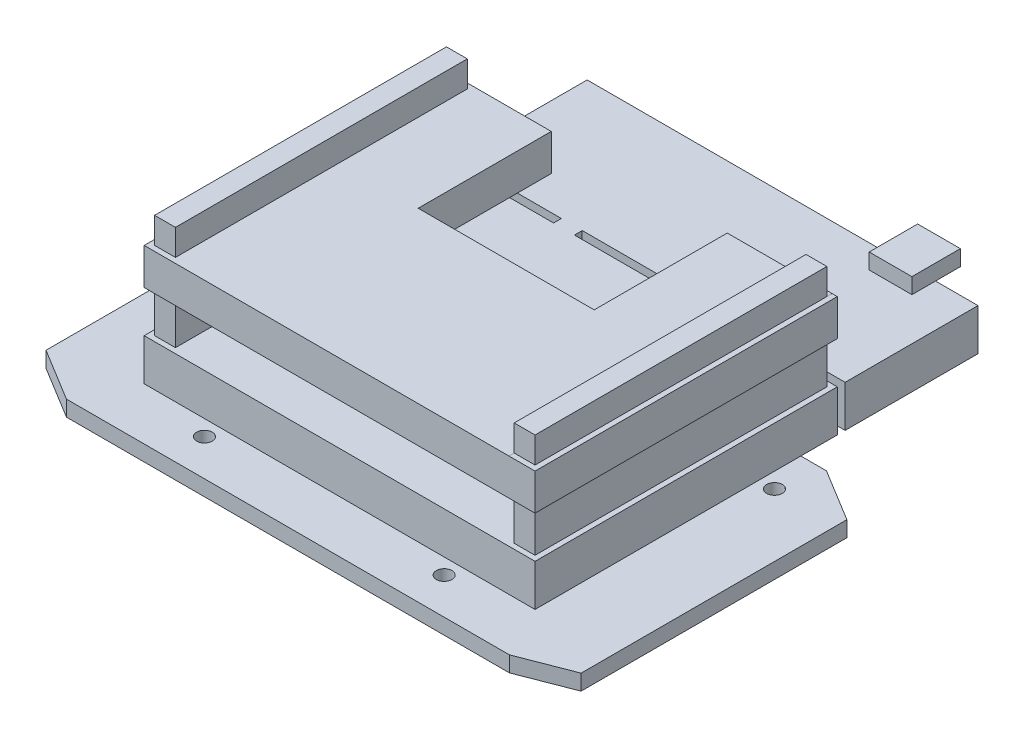
SolidWorks part; units mm, degrees
ref_plane "Front Plane" through (0, 0, 0) normal (0, 0, 1) x (1, 0, 0)
ref_plane "Top Plane" through (0, 0, 0) normal (0, 1, 0) x (1, 0, 0)
ref_plane "Right Plane" through (0, 0, 0) normal (1, 0, 0) x (0, 0, -1)
sketch "Esquisse1" plane through (0, 0, 0) normal (0, 1, 0) x (1, 0, 0)
  line L0 (-53.5603, 14.6941) -> (-43.6396, 18.5364)
  line L19 (41.3604, 18.5364) -> (51.4397, 12.3788)
  line L20 (51.4397, -38.6212) -> (41.5191, -42.4636)
  line L21 (-53.5603, -36.3059) -> (-43.4809, -42.4636)
  line L22 (-43.4809, -42.4636) -> (41.5191, -42.4636)
  line L23 (51.4397, -38.6212) -> (51.4397, 12.3788)
  line L24 (41.3604, 18.5364) -> (-43.6396, 18.5364)
  line L25 (-53.5603, 14.6941) -> (-53.5603, -36.3059)
  point P0 (0, 0)
  point P5 (0, 0)
  dimension "D1" = 105
  dimension "D2" = 85
  dimension "D3" = 85
  dimension "D4" = 51
  dimension "D5" = 51
  dimension "D7" = 61
extrude "Boss.-Extru.1" add sketch "Esquisse1" along normal blind 3
sketch "Esquisse2" plane through (0, 3, 0) normal (0, 1, 0) x (1, 0, 0)
  line L0 (-43.4809, -42.4636) -> (41.5191, -42.4636) construction
  line L1 (-0.9809, -42.4636) -> (-1.1396, 18.5364) construction
  line L2 (41.3604, 18.5364) -> (-43.6396, 18.5364) construction
  circle A0 centre (39.3813, 10.5364) radius 1.5
  circle A1 centre (-41.6187, 10.5364) radius 1.5
  circle A2 centre (-23.999, -35.4636) radius 1.5
  circle A3 centre (22.001, -35.4636) radius 1.5
  dimension "D1" = 3
  dimension "D2" = 3
  dimension "D3" = 3
  dimension "D4" = 3
  dimension "D5" = 7
  dimension "D6" = 7
  dimension "D7" = 46
  dimension "D8" = 23
  dimension "D9" = 81
  dimension "D10" = 40.5
  dimension "D11" = 8
  dimension "D12" = 8
extrude "Enlèv. mat.-Extru.1" cut sketch "Esquisse2" against normal blind 3
sketch "Esquisse3" plane through (0, 3, 0) normal (0, 1, 0) x (1, 0, 0)
  line L0 (-53.5603, 14.6941) -> (-53.5603, -36.3059) construction
  line L1 (-38.5603, -32.4636) -> (36.4397, -32.4636)
  line L2 (-38.5603, -32.4636) -> (-38.5603, 52.5364)
  line L3 (-38.5603, 52.5364) -> (36.4397, 52.5364)
  line L4 (36.4397, -32.4636) -> (36.4397, 52.5364)
  line L5 (-38.5603, -32.4636) -> (36.4397, 52.5364) construction
  line L6 (-38.5603, 52.5364) -> (36.4397, -32.4636) construction
  line L7 (-43.4809, -42.4636) -> (41.5191, -42.4636) construction
  line L8 (51.4397, -38.6212) -> (51.4397, 12.3788) construction
  point P0 (-1.0603, 10.0364)
  dimension "D1" = 85
  dimension "D2" = 75
  dimension "D3" = 15
  dimension "D4" = 10
  dimension "D5" = 15
extrude "Boss.-Extru.2" add sketch "Esquisse3" along normal blind 8
sketch "Esquisse5" plane through (0, 11, 0) normal (0, 1, 0) x (1, 0, 0)
  line L0 (36.4397, -32.4636) -> (36.4397, 52.5364) construction
  line L1 (-38.5603, -32.4636) -> (36.4397, -32.4636)
  line L2 (-38.5603, -32.4636) -> (-38.5603, 25.5364)
  line L3 (-38.5603, 25.5364) -> (36.4397, 25.5364)
  line L4 (36.4397, -32.4636) -> (36.4397, 25.5364)
  dimension "D1" = 58
extrude "Boss.-Extru.4" add sketch "Esquisse5" along normal blind 20
sketch "Esquisse6" plane through (0, 0, 0) normal (0, -1, 0) x (1, 0, 0)
  line L0 (51.4397, 13.1212) -> (-53.5603, 13.1212) construction
  line L1 (51.4397, 38.6212) -> (51.4397, -12.3788) construction
  line L2 (-53.5603, -14.6941) -> (-53.5603, 36.3059) construction
  circle A0 centre (-1.0603, 13.1212) radius 3.7838
extrude "Enlèv. mat.-Extru.2" cut sketch "Esquisse6" against normal blind 1
sketch "Esquisse8" plane through (0, 0, -25.5364) normal (0, 0, -1) x (-1, 0, 0)
  line L0 (-36.4397, 11) -> (38.5603, 11) construction
  line L1 (-31.4397, 11) -> (33.5603, 11)
  line L2 (-31.4397, 11) -> (-31.4397, 19)
  line L3 (-31.4397, 19) -> (33.5603, 19)
  line L4 (33.5603, 11) -> (33.5603, 19)
  line L5 (-36.4397, 31) -> (38.5603, 31) construction
  line L6 (-31.4397, 31) -> (33.5603, 31)
  line L7 (-31.4397, 31) -> (-31.4397, 26)
  line L8 (-31.4397, 26) -> (33.5603, 26)
  line L9 (33.5603, 31) -> (33.5603, 26)
  line L10 (-36.4397, 31) -> (-36.4397, 11) construction
  line L11 (38.5603, 31) -> (38.5603, 11) construction
  dimension "D1" = 5
  dimension "D2" = 8
  dimension "D3" = 5
  dimension "D4" = 5
  dimension "D5" = 5
  dimension "D6" = 5
extrude "Enlèv. mat.-Extru.3" cut sketch "Esquisse8" against normal blind 86
sketch "Esquisse9" plane through (-38.5603, 0, 0) normal (-1, 0, 0) x (0, 0, 1)
  line L0 (32.4636, 31) -> (32.4636, 3) construction
  line L1 (-25.5364, 11) -> (32.4636, 11)
  line L2 (-25.5364, 11) -> (-25.5364, 19)
  line L3 (-25.5364, 19) -> (32.4636, 19)
  line L4 (32.4636, 11) -> (32.4636, 19)
  line L6 (-25.5364, 31) -> (32.4636, 31)
  line L7 (-25.5364, 31) -> (-25.5364, 26)
  line L8 (-25.5364, 26) -> (32.4636, 26)
  line L9 (32.4636, 31) -> (32.4636, 26)
  dimension "D1" = 5
  dimension "D2" = 8
extrude "Enlèv. mat.-Extru.4" cut sketch "Esquisse9" against normal blind 1
sketch "Esquisse10" plane through (36.4397, 0, 0) normal (1, 0, 0) x (0, 0, -1)
  line L0 (25.5364, 31) -> (25.5364, 11) construction
  line L1 (-32.4636, 31) -> (25.5364, 31)
  line L2 (-32.4636, 31) -> (-32.4636, 25.9973)
  line L3 (-32.4636, 25.9973) -> (25.5364, 25.9973)
  line L4 (25.5364, 31) -> (25.5364, 25.9973)
  line L5 (-32.4636, 31) -> (-32.4636, 3) construction
  line L6 (25.5364, 11) -> (-32.4636, 11)
  line L7 (25.5364, 11) -> (25.5364, 19)
  line L8 (25.5364, 19) -> (-32.4636, 19)
  line L9 (-32.4636, 11) -> (-32.4636, 19)
  dimension "D1" = 5.0027
  dimension "D2" = 8
extrude "Enlèv. mat.-Extru.5" cut sketch "Esquisse10" against normal blind 1
sketch "Esquisse11" plane through (0, 0, -25.5364) normal (0, 0, -1) x (-1, 0, 0)
  line L1 (-35.4397, 31) -> (-31.4397, 31)
  line L2 (-35.4397, 31) -> (-35.4397, 26)
  line L3 (-35.4397, 26) -> (-31.4397, 26)
  line L4 (-31.4397, 31) -> (-31.4397, 26)
  line L5 (-35.4397, 19) -> (-31.4397, 19)
  line L6 (-35.4397, 19) -> (-35.4397, 11)
  line L7 (-35.4397, 11) -> (-31.4397, 11)
  line L8 (-31.4397, 19) -> (-31.4397, 11)
  line L9 (37.5603, 19) -> (33.5603, 19)
  line L10 (37.5603, 19) -> (37.5603, 11)
  line L11 (37.5603, 11) -> (33.5603, 11)
  line L12 (33.5603, 19) -> (33.5603, 11)
  line L13 (33.5603, 31) -> (37.5603, 31)
  line L14 (33.5603, 31) -> (33.5603, 26)
  line L15 (33.5603, 26) -> (37.5603, 26)
  line L16 (37.5603, 31) -> (37.5603, 26)
extrude "Enlèv. mat.-Extru.6" cut sketch "Esquisse11" against normal blind 1
sketch "Esquisse12" plane through (0, 0, 32.4636) normal (0, 0, 1) x (1, 0, 0)
  line L1 (-37.5603, 31) -> (-33.5603, 31)
  line L2 (-37.5603, 31) -> (-37.5603, 26)
  line L3 (-37.5603, 26) -> (-33.5603, 26)
  line L4 (-33.5603, 31) -> (-33.5603, 26)
  line L5 (-37.5603, 19) -> (-33.5603, 19)
  line L6 (-37.5603, 19) -> (-37.5603, 11)
  line L7 (-37.5603, 11) -> (-33.5603, 11)
  line L8 (-33.5603, 19) -> (-33.5603, 11)
  line L9 (31.4397, 31) -> (35.4397, 31)
  line L10 (31.4397, 31) -> (31.4397, 25.9973)
  line L11 (31.4397, 25.9973) -> (35.4397, 25.9973)
  line L12 (35.4397, 31) -> (35.4397, 25.9973)
  line L13 (31.4397, 19) -> (35.4397, 19)
  line L14 (31.4397, 19) -> (31.4397, 11)
  line L15 (31.4397, 11) -> (35.4397, 11)
  line L16 (35.4397, 19) -> (35.4397, 11)
extrude "Enlèv. mat.-Extru.7" cut sketch "Esquisse12" against normal blind 1
sketch "Esquisse13" plane through (0, 26, 0) normal (0, 1, 0) x (1, 0, 0)
  line L0 (35.4397, 25.5364) -> (-38.5603, 25.5364) construction
  line L1 (15.3267, 51.0728) -> (-18.4473, 51.0728)
  line L2 (15.3267, 51.0728) -> (15.3267, 0)
  line L3 (15.3267, 0) -> (-18.4473, 0)
  line L4 (-18.4473, 51.0728) -> (-18.4473, 0)
  line L5 (15.3267, 51.0728) -> (-18.4473, 0) construction
  line L6 (15.3267, 0) -> (-18.4473, 51.0728) construction
  point P0 (-1.5603, 25.5364)
extrude "Enlèv. mat.-Extru.8" cut sketch "Esquisse13" against normal blind 8
sketch "Esquisse14" plane through (0, 11, 0) normal (0, 1, 0) x (1, 0, 0)
  line L1 (-38.5603, 25.5364) -> (-18.0043, 25.5364)
  line L2 (-38.5603, 25.5364) -> (-38.5603, 27.0364)
  line L3 (-38.5603, 27.0364) -> (-18.0043, 27.0364)
  line L4 (-18.0043, 25.5364) -> (-18.0043, 27.0364)
  line L5 (36.4397, 25.5364) -> (14.5812, 25.5364)
  line L6 (36.4397, 25.5364) -> (36.4397, 27.0364)
  line L7 (36.4397, 27.0364) -> (14.5812, 27.0364)
  line L8 (14.5812, 25.5364) -> (14.5812, 27.0364)
  line L9 (-14.0043, 25.5364) -> (10.5812, 25.5364)
  line L10 (-14.0043, 25.5364) -> (-14.0043, 27.0364)
  line L11 (-14.0043, 27.0364) -> (10.5812, 27.0364)
  line L12 (10.5812, 25.5364) -> (10.5812, 27.0364)
  dimension "D1" = 1.5
  dimension "D2" = 1.5
  dimension "D3" = 1.5
  dimension "D4" = 4
  dimension "D5" = 4
extrude "Enlèv. mat.-Extru.9" cut sketch "Esquisse14" against normal blind 8
sketch "Esquisse15" plane through (0, 11, 0) normal (0, 1, 0) x (1, 0, 0)
  line L1 (20.0921, 48.0056) -> (28.2872, 48.0056)
  line L2 (20.0921, 48.0056) -> (20.0921, 57.3082)
  line L3 (20.0921, 57.3082) -> (28.2872, 57.3082)
  line L4 (28.2872, 48.0056) -> (28.2872, 57.3082)
extrude "Boss.-Extru.5" add sketch "Esquisse15" along normal blind 3
